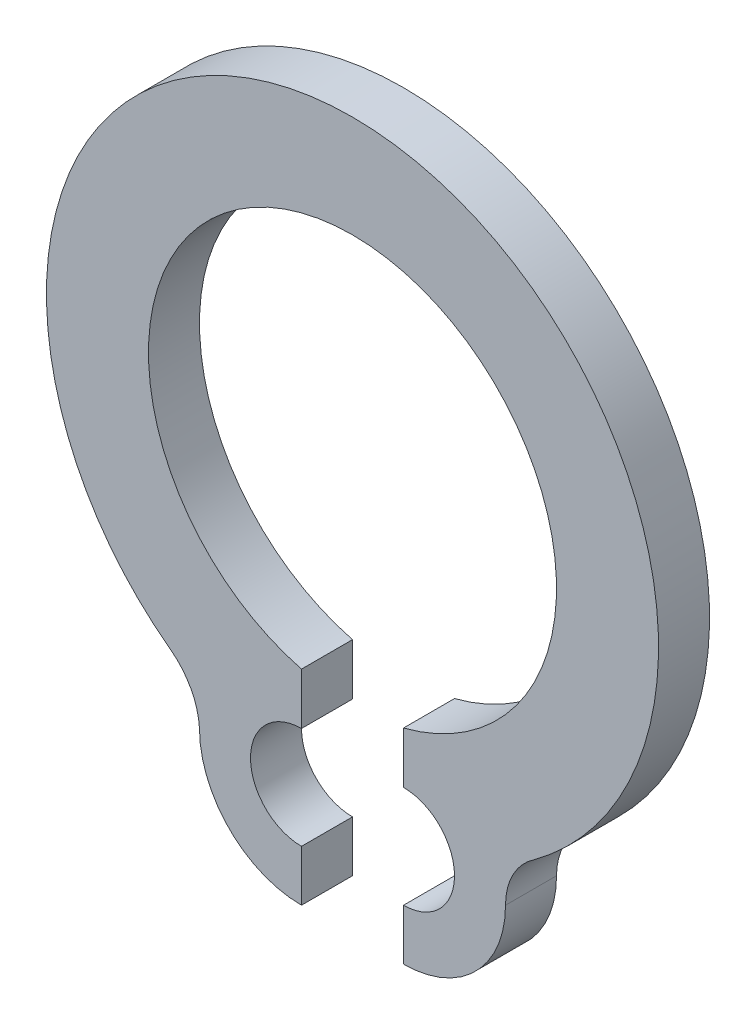
SolidWorks part; units mm, degrees
ref_plane "Alzado" through (0, 0, 0) normal (0, 0, 1) x (1, 0, 0)
ref_plane "Planta" through (0, 0, 0) normal (0, 1, 0) x (1, 0, 0)
ref_plane "Vista lateral" through (0, 0, 0) normal (1, 0, 0) x (0, 0, -1)
sketch "Croquis1" plane through (0, 0, 0) normal (0, 0, 1) x (1, 0, 0)
  line L1 (0.5, -2.441) -> (0.5, -1.9365)
  line L4 (0.5, -1.9365) -> (0.5, -2.441) construction
  line L6 (0.5, -3.441) -> (0.5, -3.941) construction
  line L10 (0, 0) -> (0, -50000) construction
  line L13 (0.5, -3.441) -> (0.5, -3.941)
  line L20 (-0.5, -3.441) -> (-0.5, -3.941) construction
  line L22 (-0.5, -1.9365) -> (-0.5, -2.441) construction
  line L23 (-0.5, -2.441) -> (-0.5, -1.9365)
  line L24 (-0.5, -3.441) -> (-0.5, -3.941)
  arc A4 (0.5, -3.941) -> (1.5, -2.941) centre (0.5, -2.941) ccw
  arc A5 (-0.5, -3.941) -> (-1.5, -2.941) centre (-0.5, -2.941) cw
  arc A6 (-0.5, -2.441) -> (-0.5, -3.441) centre (-0.5, -2.941) ccw
  arc A8 (-1.7867, -2.4099) -> (1.7867, -2.4099) centre (0, 0) cw
  arc A9 (-0.5, -1.9365) -> (0.5, -1.9365) centre (0, 0) cw
  arc A10 (1.5, -2.941) -> (1.7867, -2.4099) centre (2.1353, -2.941) cw
  arc A11 (-1.7867, -2.4099) -> (-1.5, -2.941) centre (-2.2106, -2.9817) cw
  arc A12 (0.5, -2.441) -> (0.5, -3.441) centre (0.5, -2.941) cw
  point P6 (0, 0)
extrude "Saliente-Extruir1" add sketch "Croquis1" along normal blind 0.5
